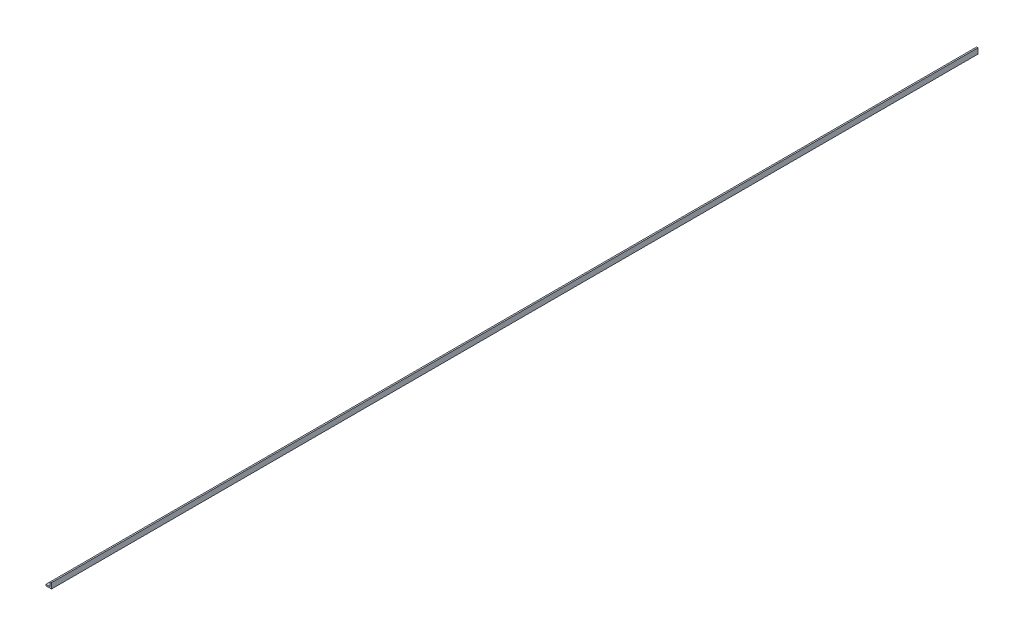
SolidWorks part; units mm, degrees
material "6063-T4"
ref_plane "Front Plane" through (0, 0, 0) normal (0, 0, 1) x (1, 0, 0)
ref_plane "Top Plane" through (0, 0, 0) normal (0, 1, 0) x (1, 0, 0)
ref_plane "Right Plane" through (0, 0, 0) normal (1, 0, 0) x (0, 0, -1)
sketch "Sketch2" plane through (0, 0, 0) normal (0, 0, 1) x (1, 0, 0)
  line L0 (-6.35, 0) -> (6.35, 0)
  line L1 (6.35, 0) -> (6.35, 12.7)
  line L2 (6.35, 12.7) -> (3.175, 12.7)
  line L3 (3.175, 12.7) -> (3.175, 3.175)
  line L4 (3.175, 3.175) -> (-6.35, 3.175)
  line L5 (-6.35, 0) -> (-6.35, 3.175)
  line L6 (4.7625, 12.7) -> (6.35, 12.7) construction
  line L7 (-6.35, 1.5875) -> (-6.35, 0) construction
  dimension "Vert" = 12.7
  dimension "Horz" = 12.7
  dimension "Thickness" = 3.175
extrude "Boss-Extrude1" add sketch "Sketch2" along normal mid plane 2133.6
